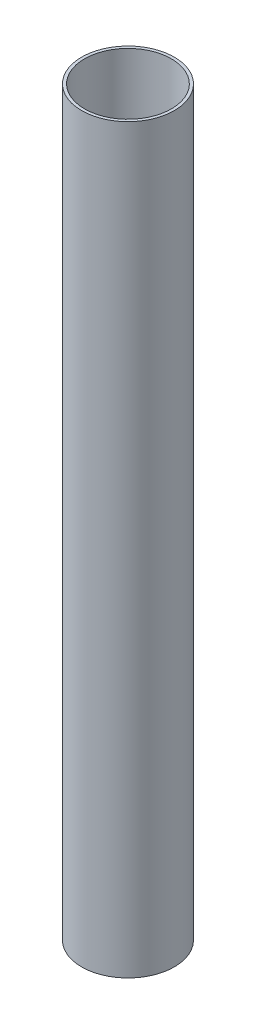
SolidWorks part; units mm, degrees
ref_plane "Front Plane" through (0, 0, 0) normal (0, 0, 1) x (1, 0, 0)
ref_plane "Top Plane" through (0, 0, 0) normal (0, 1, 0) x (1, 0, 0)
ref_plane "Right Plane" through (0, 0, 0) normal (1, 0, 0) x (0, 0, -1)
sketch "Sketch1" plane through (0, 0, 0) normal (0, 1, 0) x (1, 0, 0)
  circle A0 centre (0, 0) radius 6.35
  circle A1 centre (0, 0) radius 5.9495
  dimension "D1" = 12.7
  dimension "D2" = 11.899
sketch "Sketch2" plane through (0, 0, 0) normal (1, 0, 0) x (0, 0, -1)
  line L0 (0, 0) -> (0, 101.6)
  dimension "D1" = 101.6
sweep "Sweep1" add profiles "Sketch1" path "Sketch2"
